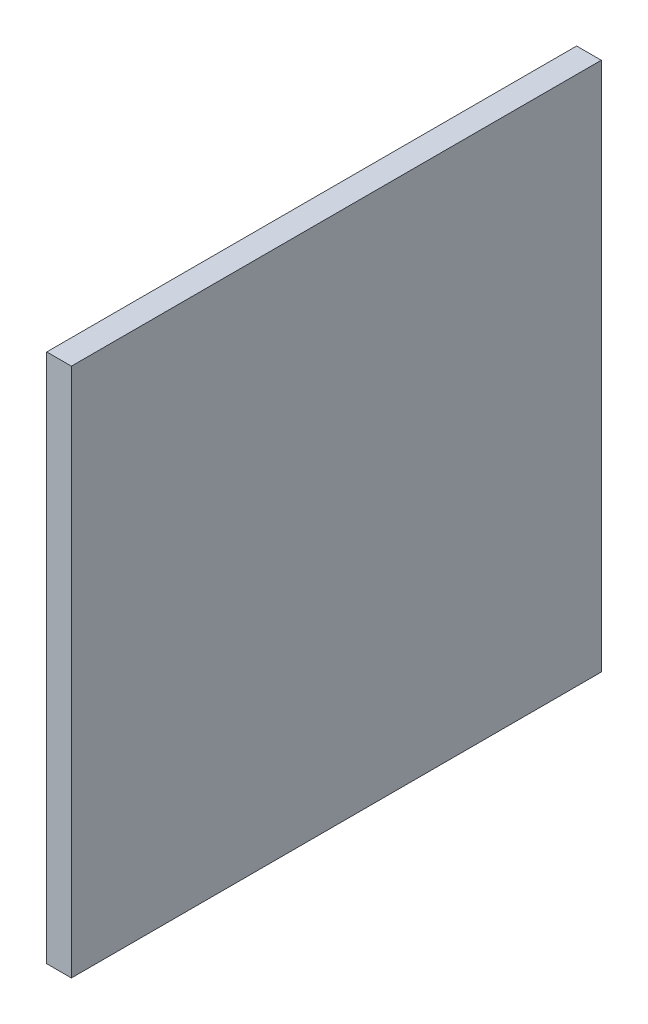
SolidWorks part; units mm, degrees
ref_plane "Front Plane" through (0, 0, 0) normal (0, 0, 1) x (1, 0, 0)
ref_plane "Top Plane" through (0, 0, 0) normal (0, 1, 0) x (1, 0, 0)
ref_plane "Right Plane" through (0, 0, 0) normal (1, 0, 0) x (0, 0, -1)
sketch "Sketch2" plane through (0, 0, 0) normal (1, 0, 0) x (0, 0, -1)
  line L0 (0, 0) -> (0, 43)
  line L1 (0, 43) -> (43, 43)
  line L2 (43, 43) -> (43, 0)
  line L3 (43, 0) -> (0, 0)
extrude "Boss-Extrude1" add sketch "Sketch2" along normal blind 2
sketch "Sketch3" plane through (0, 0, 0) normal (1, 0, 0) x (0, 0, -1)
  circle A0 centre (6.1, 36.6575) radius 1.5
  circle A1 centre (10.4, 36.6575) radius 1.5
  circle A2 centre (14.7, 36.6575) radius 1.5
  circle A3 centre (19, 36.6575) radius 1.5
  circle A4 centre (23.3, 36.6575) radius 1.5
  circle A5 centre (27.6, 36.6575) radius 1.5
  circle A7 centre (31.93, 36.6575) radius 1.5
  circle A8 centre (36.23, 36.6575) radius 1.5
  point P0 (0, 0)
extrude "Boss-Extrude5" add sketch "Sketch3" against normal blind 4
sketch "Sketch5" plane through (0, 0, 0) normal (1, 0, 0) x (0, 0, -1)
  circle A0 centre (36.23, 32.3549) radius 1.5
  circle A1 centre (31.9336, 32.3549) radius 1.5
  circle A2 centre (27.6336, 32.3549) radius 1.5
  circle A3 centre (23.3336, 32.3549) radius 1.5
  circle A4 centre (19.0336, 32.3549) radius 1.5
  circle A5 centre (14.7336, 32.3549) radius 1.5
  circle A6 centre (10.4336, 32.3549) radius 1.5
  circle A7 centre (6.1336, 32.3549) radius 1.5
  circle A8 centre (6.1336, 28.0549) radius 1.51
  circle A9 centre (10.4336, 28.0549) radius 1.5
  circle A10 centre (14.7336, 28.0549) radius 1.5
  circle A11 centre (19.0336, 28.0549) radius 1.5
  circle A12 centre (23.3336, 28.0549) radius 1.5
  circle A13 centre (27.6336, 28.0549) radius 1.5
  circle A14 centre (31.9336, 28.0549) radius 1.5
  circle A15 centre (36.23, 28.0549) radius 1.5
  circle A16 centre (36.23, 23.7549) radius 1.5
  circle A17 centre (31.9336, 23.7549) radius 1.5
  circle A18 centre (27.6336, 23.7549) radius 1.5
  circle A19 centre (23.3336, 23.7549) radius 1.5
  circle A20 centre (19.0336, 23.7549) radius 1.5
  circle A21 centre (14.7336, 23.7549) radius 1.5
  circle A22 centre (10.4336, 23.7549) radius 1.5
  circle A23 centre (6.1336, 23.7549) radius 1.5
  circle A24 centre (6.1336, 19.4549) radius 1.5
  circle A25 centre (10.4336, 19.4549) radius 1.5
  circle A26 centre (14.7336, 19.4549) radius 1.5
  circle A28 centre (19.0336, 19.4549) radius 1.5
  circle A29 centre (23.3336, 19.4549) radius 1.5
  circle A30 centre (27.6336, 19.4549) radius 1.5
  circle A31 centre (31.9336, 19.4549) radius 1.5
  circle A32 centre (36.23, 19.4549) radius 1.5
  circle A33 centre (36.23, 15.1549) radius 1.5
  circle A34 centre (31.9336, 15.1549) radius 1.5
  circle A35 centre (27.6336, 15.1549) radius 1.5
  circle A36 centre (23.3336, 15.1549) radius 1.5
  circle A38 centre (19.0336, 15.1549) radius 1.5
  circle A39 centre (14.7336, 15.1549) radius 1.5
  circle A40 centre (10.4336, 15.1549) radius 1.5
  circle A41 centre (6.1336, 15.1549) radius 1.5
  circle A42 centre (6.1336, 10.8549) radius 1.5
  circle A43 centre (10.4336, 10.8549) radius 1.5
  circle A44 centre (14.7336, 10.8549) radius 1.5
  circle A45 centre (19.0336, 10.8549) radius 1.5
  circle A46 centre (23.3336, 10.8549) radius 1.5
  circle A47 centre (27.6336, 10.8549) radius 1.5
  circle A48 centre (31.9336, 10.8549) radius 1.5
  circle A49 centre (36.23, 10.8549) radius 1.5
  circle A50 centre (36.23, 6.5549) radius 1.5
  circle A51 centre (31.9336, 6.5549) radius 1.5
  circle A52 centre (27.6336, 6.5549) radius 1.5
  circle A53 centre (23.3336, 6.5549) radius 1.5
  circle A54 centre (19.0336, 6.5549) radius 1.5
  circle A55 centre (14.7336, 6.5549) radius 1.5
  circle A56 centre (10.4336, 6.5549) radius 1.5
  circle A57 centre (6.1336, 6.5549) radius 1.5
extrude "Boss-Extrude6" add sketch "Sketch5" against normal blind 4 separate body
fillet "Fillet3" radius 1 1 edges at (-4, 36.6575, -37.73)
fillet "Fillet4" radius 1 7 edges at (-4, 36.6575, -7.6) (-4, 36.6575, -33.43) (-4, 36.6575, -11.9) (-4, 36.6575, -16.2) (-4, 36.6575, -20.5) (-4, 36.6575, -24.8) (-4, 36.6575, -29.1)
fillet "Fillet5" radius 1 1 edges at (-4, 32.3549, -37.73)
fillet "Fillet6" radius 1 1 edges at (-4, 32.3549, -33.4336)
fillet "Fillet7" radius 1 1 edges at (-4, 32.3549, -29.1336)
fillet "Fillet8" radius 1 1 edges at (-4, 32.3549, -24.8336)
fillet "Fillet9" radius 1 1 edges at (-4, 32.3549, -20.5336)
fillet "Fillet10" radius 1 1 edges at (-4, 32.3549, -16.2336)
fillet "Fillet11" radius 1 1 edges at (-4, 32.3549, -11.9336)
fillet "Fillet12" radius 1 1 edges at (-4, 32.3549, -7.6336)
fillet "Fillet13" radius 1 1 edges at (-4, 28.0549, -37.73)
fillet "Fillet14" radius 1 1 edges at (-4, 28.0549, -33.4336)
fillet "Fillet15" radius 1 1 edges at (-4, 28.0549, -29.1336)
fillet "Fillet16" radius 1 1 edges at (-4, 28.0549, -24.8336)
fillet "Fillet17" radius 1 1 edges at (-4, 28.0549, -20.5336)
fillet "Fillet18" radius 1 1 edges at (-4, 28.0549, -16.2336)
fillet "Fillet19" radius 1 1 edges at (-4, 28.0549, -7.6436)
fillet "Fillet20" radius 1 1 edges at (-4, 28.0549, -11.9336)
fillet "Fillet21" radius 1 1 edges at (-4, 23.7549, -11.9336)
fillet "Fillet22" radius 1 1 edges at (-4, 23.7549, -7.6336)
fillet "Fillet23" radius 1 1 edges at (-4, 23.7549, -16.2336)
fillet "Fillet24" radius 1 1 edges at (-4, 23.7549, -20.5336)
fillet "Fillet25" radius 1 1 edges at (-4, 23.7549, -24.8336)
fillet "Fillet26" radius 1 1 edges at (-4, 23.7549, -29.1336)
fillet "Fillet27" radius 1 1 edges at (-4, 23.7549, -33.4336)
fillet "Fillet28" radius 1 1 edges at (-4, 23.7549, -37.73)
fillet "Fillet29" radius 1 1 edges at (-4, 19.4549, -37.73)
fillet "Fillet30" radius 1 1 edges at (-4, 19.4549, -33.4336)
fillet "Fillet31" radius 1 1 edges at (-4, 19.4549, -29.1336)
fillet "Fillet32" radius 1 1 edges at (-4, 19.4549, -24.8336)
fillet "Fillet33" radius 1 1 edges at (-4, 19.4549, -20.5336)
fillet "Fillet34" radius 1 1 edges at (-4, 19.4549, -16.2336)
fillet "Fillet35" radius 1 1 edges at (-4, 19.4549, -11.9336)
fillet "Fillet36" radius 1 2 edges at (0, 19.4549, -7.6336) (-4, 19.4549, -7.6336)
fillet "Fillet37" radius 1 1 edges at (-4, 15.1549, -7.6336)
fillet "Fillet38" radius 1 1 edges at (-4, 15.1549, -11.9336)
fillet "Fillet39" radius 1 1 edges at (-4, 15.1549, -16.2336)
fillet "Fillet40" radius 1 1 edges at (-4, 15.1549, -20.5336)
fillet "Fillet41" radius 1 1 edges at (-4, 15.1549, -24.8336)
fillet "Fillet42" radius 1 1 edges at (-4, 15.1549, -29.1336)
fillet "Fillet43" radius 1 1 edges at (-4, 15.1549, -33.4336)
fillet "Fillet44" radius 1 1 edges at (-4, 15.1549, -37.73)
fillet "Fillet45" radius 1 1 edges at (-4, 10.8549, -37.73)
fillet "Fillet46" radius 1 1 edges at (-4, 10.8549, -33.4336)
fillet "Fillet47" radius 1 1 edges at (-4, 10.8549, -29.1336)
fillet "Fillet48" radius 1 1 edges at (-4, 10.8549, -24.8336)
fillet "Fillet49" radius 1 1 edges at (-4, 10.8549, -20.5336)
fillet "Fillet50" radius 1 1 edges at (-4, 10.8549, -16.2336)
fillet "Fillet51" radius 1 1 edges at (-4, 10.8549, -11.9336)
fillet "Fillet52" radius 1 1 edges at (-4, 10.8549, -7.6336)
fillet "Fillet53" radius 1 1 edges at (-4, 6.5549, -11.9336)
fillet "Fillet54" radius 1 1 edges at (-4, 6.5549, -7.6336)
fillet "Fillet55" radius 1 1 edges at (-4, 6.5549, -16.2336)
fillet "Fillet56" radius 1 1 edges at (-4, 6.5549, -20.5336)
fillet "Fillet57" radius 1 1 edges at (-4, 6.5549, -29.1336)
fillet "Fillet58" radius 1 1 edges at (-4, 6.5549, -33.4336)
fillet "Fillet59" radius 1 1 edges at (-4, 6.5549, -37.73)
fillet "Fillet60" radius 1 1 edges at (-4, 6.5549, -24.8336)
